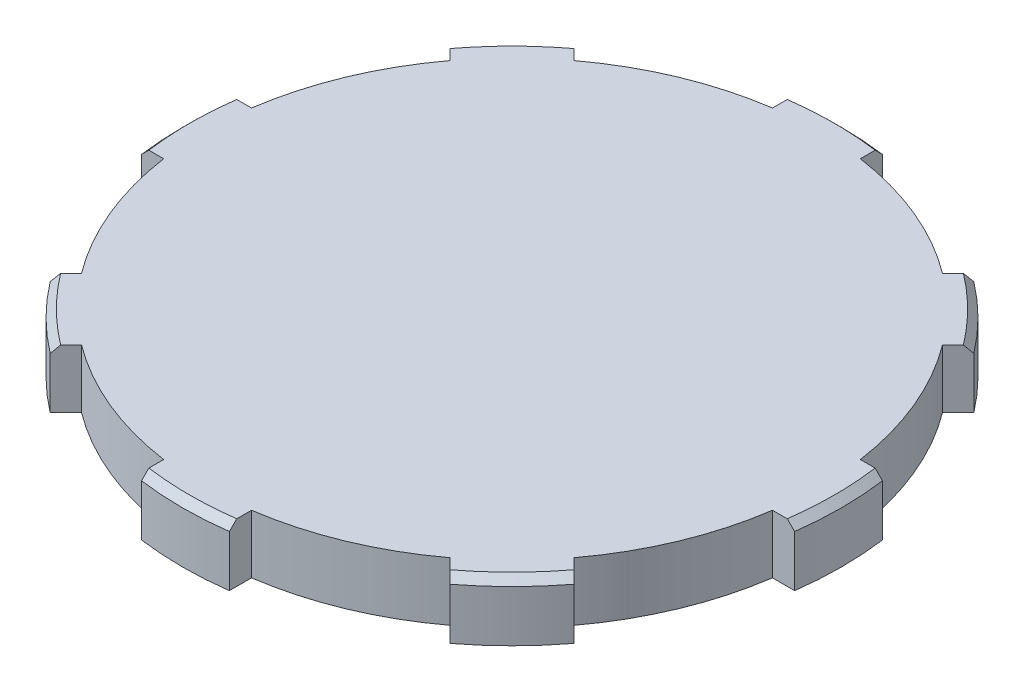
SolidWorks part; units mm, degrees
ref_plane "前视基准面" through (0, 0, 0) normal (0, 0, 1) x (1, 0, 0)
ref_plane "上视基准面" through (0, 0, 0) normal (0, 1, 0) x (1, 0, 0)
ref_plane "右视基准面" through (0, 0, 0) normal (1, 0, 0) x (0, 0, -1)
sketch "草图1" plane through (0, 0, 0) normal (0, 1, 0) x (1, 0, 0)
  circle A0 centre (0, 0) radius 21
  dimension "D1" = 42
extrude "凸台-拉伸1" add sketch "草图1" along normal blind 4
sketch "草图2" plane through (0, 4, 0) normal (0, 1, 0) x (1, 0, 0)
  line L1 (-22.2991, 3) -> (22.2991, 3)
  line L3 (-22.2991, -3) -> (22.2991, -3)
  line L5 (-22.3617, 2.4909) -> (22.3617, -2.4909) construction
  line L6 (-22.3617, -2.4909) -> (22.3617, 2.4909) construction
  arc A0 (-22.2991, 3) -> (-22.2991, -3) centre (0, 0) ccw
  arc A1 (22.2991, -3) -> (22.2991, 3) centre (0, 0) ccw
  dimension "D1" = 45
extrude "凸台-拉伸2" add sketch "草图2" against normal blind 4
pattern_circular "阵列(圆周)1" count 8 over 360 about axis through (0, 0, 0) along (0, 1, 0) of "凸台-拉伸2"
chamfer "倒角1" distance 0.5 angle 45 8 edges at (22.5, 4, 0) (-22.5, 4, 0) (15.9099, 4, -15.9099) (0, 4, -22.5) (-15.9099, 4, -15.9099) (15.9099, 4, 15.9099) (-15.9099, 4, 15.9099) (0, 4, 22.5)
